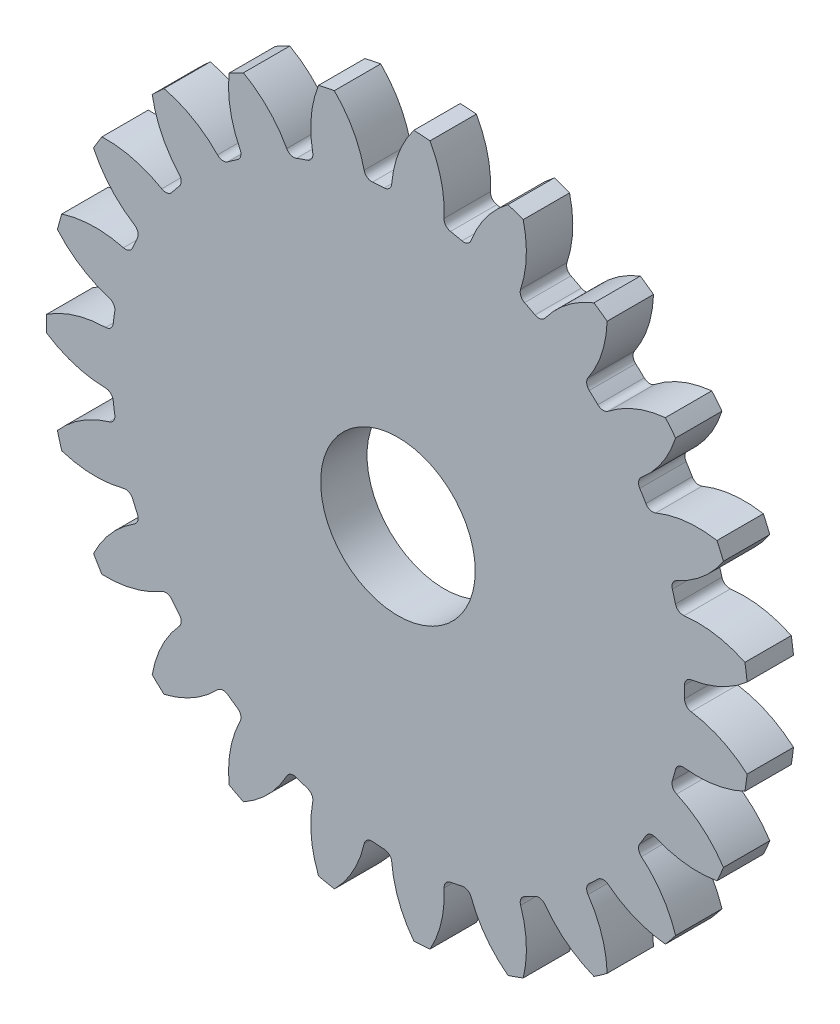
SolidWorks part; units mm, degrees
ref_plane "Alzado" through (0, 0, 0) normal (0, 0, 1) x (1, 0, 0)
ref_plane "Planta" through (0, 0, 0) normal (0, 1, 0) x (1, 0, 0)
ref_plane "Vista lateral" through (0, 0, 0) normal (1, 0, 0) x (0, 0, -1)
sketch "Croquis1" plane through (0, 0, 0) normal (0, 0, 1) x (1, 0, 0)
  circle A0 centre (0, 0) radius 22.733
  dimension "D1" = 45.466
extrude "Saliente-Extruir1" add sketch "Croquis1" along normal blind 3
sketch "Croquis2" plane through (0, 0, 3) normal (0, 0, 1) x (1, 0, 0)
  line L0 (0, 0) -> (0, 20.828) construction
  line L1 (0, 0) -> (8.1237, 22.3197) construction
  line L2 (0, 0) -> (-1.4224, 20.7794) construction
  line L3 (0, 20.828) -> (6.694, 18.3916) construction
  arc A0 (1.0284, 22.7097) -> (-4.1134, 22.3578) centre (0, 0) ccw
  arc A2 (-0.4281, 18.5371) -> (-2.1019, 18.4225) centre (0, 0) ccw
  arc A3 (1.0284, 22.7097) -> (-0.4281, 18.5371) centre (6.694, 18.3916) ccw
  arc A4 (-4.1134, 22.3578) -> (-2.1019, 18.4225) centre (-9.1377, 17.3079) cw
  dimension "D2" = 37.084
  dimension "D3" = 20
  dimension "D4" = 1.4224
extrude "Cortar-Extruir1" cut sketch "Croquis2" against normal through all
fillet "Redondeo1" radius 0.508 2 edges at (-0.4281, 18.5371, 1.5) (-2.1019, 18.4225, 1.5)
pattern_circular "MatrizC1" count 23 over 360 about axis through (0, 0, 0) along (0, 0, 1) of "Redondeo1", "Cortar-Extruir1"
sketch "Croquis3" plane through (0, 0, 3) normal (0, 0, 1) x (1, 0, 0)
  circle A0 centre (0, 0) radius 5
  dimension "D1" = 10
extrude "Cortar-Extruir2" cut sketch "Croquis3" against normal through all
